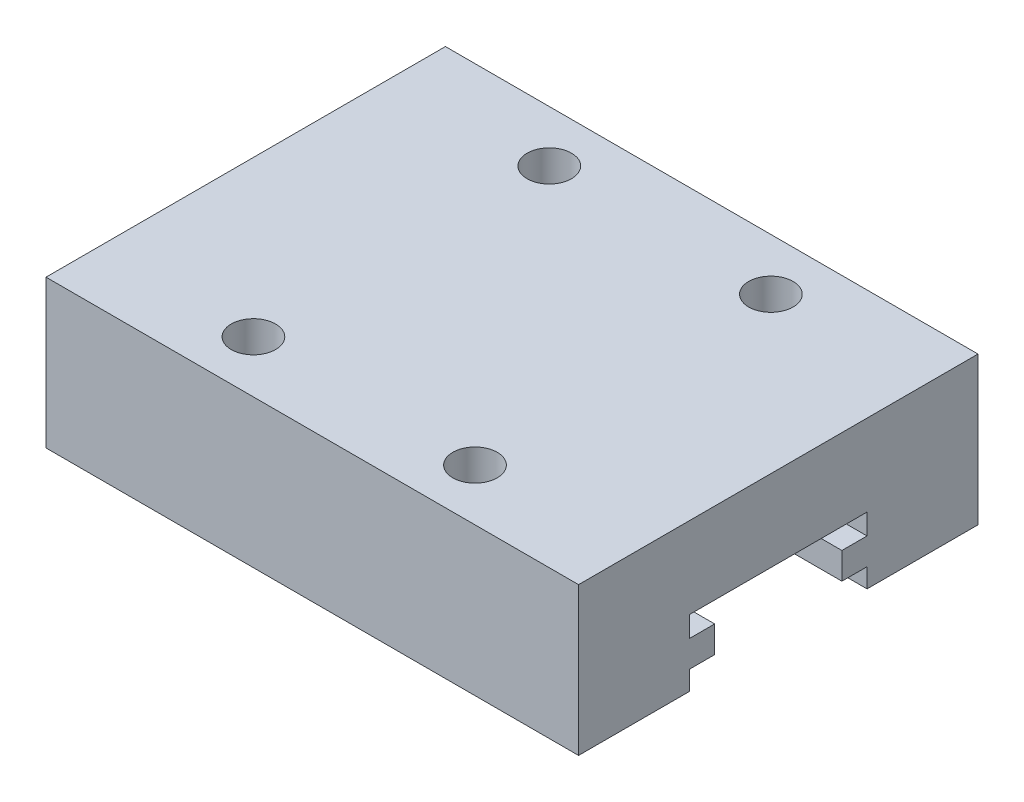
SolidWorks part; units mm, degrees
ref_plane "Alzado" through (0, 0, 0) normal (0, 0, 1) x (1, 0, 0)
ref_plane "Planta" through (0, 0, 0) normal (0, 1, 0) x (1, 0, 0)
ref_plane "Vista lateral" through (0, 0, 0) normal (1, 0, 0) x (0, 0, -1)
sketch "Croquis1" plane through (0, 0, 0) normal (0, 1, 0) x (1, 0, 0)
  line L2 (0, 0) -> (36, 0)
  line L3 (0, 0) -> (0, 27)
  line L4 (0, 27) -> (36, 27)
  line L5 (36, 0) -> (36, 27)
  dimension "D1" = 36
  dimension "D2" = 27
extrude "Saliente-Extruir1" add sketch "Croquis1" along normal blind 10
sketch "Croquis2" plane through (0, 10, 0) normal (0, 1, 0) x (1, 0, 0)
  line L0 (0, 0) -> (36, 0) construction
  line L2 (18, 0) -> (18, 27) construction
  line L3 (36, 27) -> (0, 27) construction
  circle A0 centre (10.5, 23.5201) radius 1.5
  circle A1 centre (25.5, 23.5) radius 1.5
  circle A2 centre (10.5, 3.5201) radius 1.5
  circle A3 centre (25.5, 3.5) radius 1.5
  dimension "D1" = 3
  dimension "D2" = 15
  dimension "D3" = 15
  dimension "D4" = 20
  dimension "D5" = 20
  dimension "D6" = 3.5
  dimension "D7" = 7.5
  dimension "D8" = 15
  dimension "D9" = 7.5
extrude "Cortar-Extruir1" cut sketch "Croquis2" against normal blind 5
sketch "Croquis3" plane through (36, 0, 0) normal (1, 0, 0) x (0, 0, -1)
  line L0 (0, 0) -> (27, 0) construction
  line L1 (7.5, 0) -> (19.5, 0)
  line L2 (7.5, 0) -> (7.5, 1.3)
  line L3 (7.5, 4.5) -> (19.5, 4.5)
  line L4 (19.5, 0) -> (19.5, 1.3)
  line L5 (13.5, 10) -> (13.5, 0) construction
  line L6 (0, 10) -> (27, 10) construction
  line L7 (7.5, 3.1) -> (7.5, 4.5)
  line L8 (7.5, 3.1) -> (9.2, 3.1)
  line L10 (7.5, 1.3) -> (9.2, 1.3)
  line L11 (9.2, 3.1) -> (9.2, 1.3)
  line L12 (19.5, 1.3) -> (17.8, 1.3)
  line L13 (19.5, 3.1) -> (17.8, 3.1)
  line L14 (17.8, 3.1) -> (17.8, 1.3)
  line L15 (19.5, 3.1) -> (19.5, 4.5)
  dimension "D2" = 4.5
  dimension "D3" = 6
  dimension "D4" = 1.8
  dimension "D5" = 1.7
  dimension "D6" = 1.4
extrude "Cortar-Extruir2" cut sketch "Croquis3" against normal up to surface (36 mm away) up to face at (0, 5, -13.5)
